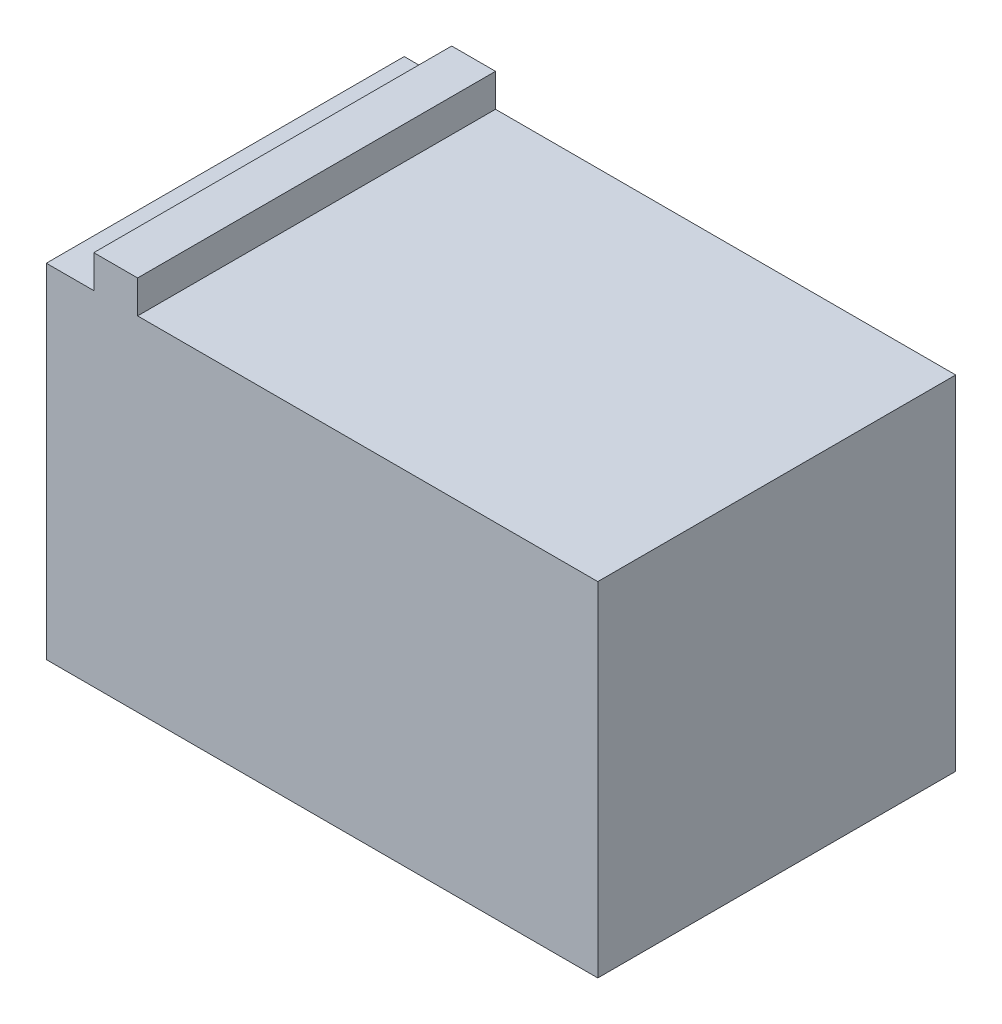
SolidWorks part; units mm, degrees
ref_plane "Спереди" through (0, 0, 0) normal (0, 0, 1) x (1, 0, 0)
ref_plane "Сверху" through (0, 0, 0) normal (0, 1, 0) x (1, 0, 0)
ref_plane "Справа" through (0, 0, 0) normal (1, 0, 0) x (0, 0, -1)
sketch "Эскиз1" plane through (0, 0, 0) normal (0, 1, 0) x (1, 0, 0)
  line L1 (-75.5, -49) -> (75.5, -49)
  line L2 (-75.5, -49) -> (-75.5, 49)
  line L3 (-75.5, 49) -> (75.5, 49)
  line L4 (75.5, -49) -> (75.5, 49)
  line L5 (-75.5, -49) -> (75.5, 49) construction
  line L6 (-75.5, 49) -> (75.5, -49) construction
  point P0 (0, 0)
  dimension "D1" = 151
  dimension "D2" = 98
extrude "Бобышка-Вытянуть1" add sketch "Эскиз1" along normal blind 94
sketch "Эскиз2" plane through (0, 94, 0) normal (0, 1, 0) x (1, 0, 0)
  line L0 (75.5, 49) -> (-75.5, 49) construction
  line L1 (-62.5, 49) -> (-50.5, 49)
  line L2 (-62.5, 49) -> (-62.5, -49)
  line L3 (-62.5, -49) -> (-50.5, -49)
  line L4 (-50.5, 49) -> (-50.5, -49)
  line L5 (-75.5, -49) -> (75.5, -49) construction
  line L6 (-75.5, 49) -> (-75.5, -49) construction
  dimension "D1" = 13
  dimension "D2" = 12
extrude "Бобышка-Вытянуть2" add sketch "Эскиз2" along normal blind 9
